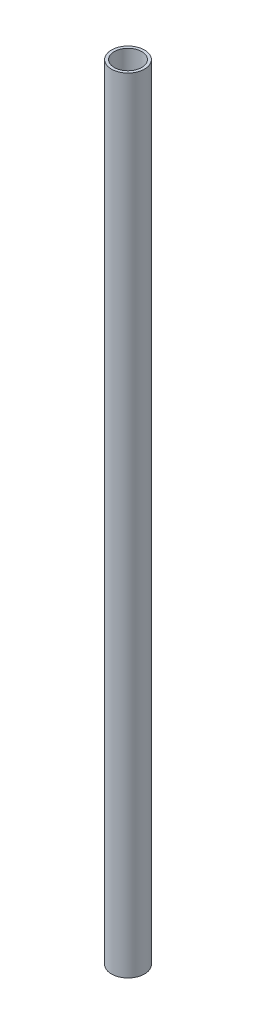
SolidWorks part; units mm, degrees
ref_plane "Front Plane" through (0, 0, 0) normal (0, 0, 1) x (1, 0, 0)
ref_plane "Top Plane" through (0, 0, 0) normal (0, 1, 0) x (1, 0, 0)
ref_plane "Right Plane" through (0, 0, 0) normal (1, 0, 0) x (0, 0, -1)
sketch "Sketch1" plane through (0, 0, 0) normal (0, 1, 0) x (1, 0, 0)
  circle A0 centre (0, 0) radius 21.082
  circle A1 centre (0, 0) radius 17.526
  dimension "D1" = 42.164
  dimension "D2" = 35.052
extrude "Boss-Extrude1" add sketch "Sketch1" along normal blind 996.95
